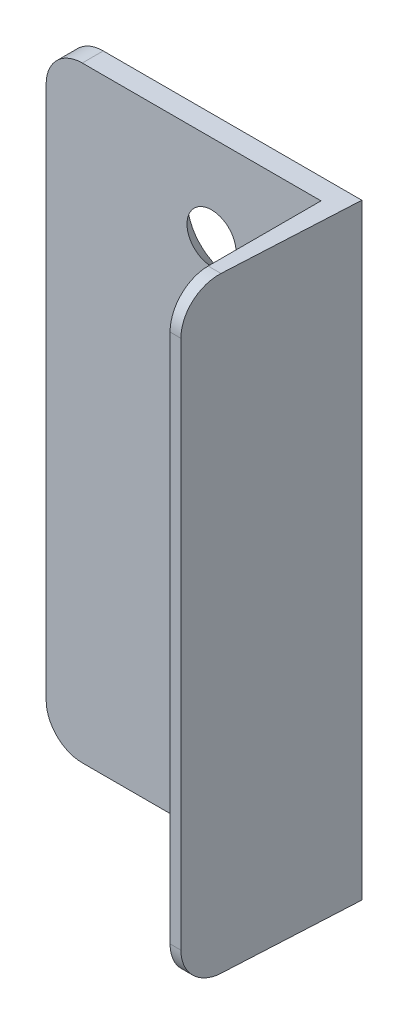
SolidWorks part; units mm, degrees
material "Brass"
ref_plane "Top Plane" through (0, 0, 0) normal (0, 0, 1) x (1, 0, 0)
ref_plane "Front Plane" through (0, 0, 0) normal (0, 1, 0) x (1, 0, 0)
ref_plane "Right Plane" through (0, 0, 0) normal (1, 0, 0) x (0, 0, -1)
sketch "Sketch1" plane through (0, 0, 0) normal (0, 0, 1) x (1, 0, 0)
  line L1 (-15.4, -41.95) -> (20.4, -41.95)
  line L2 (-20.4, -36.95) -> (-20.4, 36.95)
  line L3 (-15.4, 41.95) -> (20.4, 41.95)
  line L4 (20.4, -41.95) -> (20.4, 41.95)
  line L5 (-20.4, -41.95) -> (20.4, 41.95) construction
  line L6 (-20.4, 41.95) -> (20.4, -41.95) construction
  arc A0 (-20.4, -36.95) -> (-15.4, -41.95) centre (-15.4, -36.95) ccw
  arc A1 (-15.4, 41.95) -> (-20.4, 36.95) centre (-15.4, 36.95) ccw
  point P0 (0, 0)
  dimension "D3" = 5
  dimension "D1" = 40.8
  dimension "D2" = 83.9
extrude "Boss-Extrude1" add sketch "Sketch1" along normal blind 2.9
sketch "Sketch2" plane through (0, 0, 2.9) normal (0, 0, 1) x (1, 0, 0)
  line L0 (-15.4, -41.95) -> (20.4, -41.95) construction
  line L1 (20.4, 41.95) -> (17.65, 41.95)
  line L2 (20.4, 41.95) -> (20.4, -41.95)
  line L3 (20.4, -41.95) -> (17.65, -41.95)
  line L4 (17.65, 41.95) -> (17.65, -41.95)
  dimension "D1" = 2.75
extrude "Boss-Extrude2" add sketch "Sketch2" along normal blind 20.9
sketch "Sketch4" plane through (20.4, 0, 0) normal (1, 0, 0) x (0, 0, -1)
  line L16 (-23.8, 36.6765) -> (-23.8, 41.95)
  line L21 (-23.8, 41.95) -> (-18.5265, 41.95)
  line L22 (-23.8, -41.95) -> (-23.8, -36.6765)
  line L23 (-23.8, -41.95) -> (-18.5265, -41.95)
  arc A4 (-18.5265, -41.95) -> (-23.8, -36.6765) centre (-18.5265, -36.6765) cw
  arc A5 (-18.5265, 41.95) -> (-23.8, 36.6765) centre (-18.5265, 36.6765) ccw
  point P3 (-23.8, 41.95)
  point P8 (-23.8, -41.95)
  dimension "D1" = 5.2735
  dimension "D2" = 7.4578
  dimension "D3" = 7.4578
extrude "Cut-Extrude1" cut sketch "Sketch4" against normal blind 27.75
sketch "Sketch5" plane through (0, 0, 0) normal (0, 0, -1) x (-1, 0, 0)
  line L1 (-2.5, -41.95) -> (-2.5, 41.95) construction
  line L2 (15.4, -41.95) -> (-20.4, -41.95) construction
  line L3 (-20.4, 41.95) -> (15.4, 41.95) construction
  point P0 (-2.5, 29.8957)
  point P2 (-2.5, -29.8957)
  dimension "D1" = 30
  dimension "D2" = 30
hole_wizard "CSK for M6 Flat Head Machine Screw1" positions "Sketch5" profile "Sketch6" countersink size "M6" standard "ANSI Metric" end condition up to next
sketch "Sketch6" plane through (2.5, 29.8957, 0) normal (1, 0, 0) x (0, 1, 0)
  line L0 (0, 0) -> (0, 2.9)
  line L1 (0, 2.9) -> (3.3, 2.9)
  line L2 (3.3, 2.9) -> (3.3, 3)
  line L3 (3.3, 3) -> (6.3, 0)
  line L5 (6.3, 0) -> (0, 0)
  line L6 (-3.3, 3) -> (-6.3, 0) construction
  line L11 (0, -6.35) -> (0, 107.95) construction
  dimension "Thru Hole Dia." = 6.6
  dimension "Thru Hole Depth" = 2.9
  dimension "Near C'Sink Dia." = 12.6
  dimension "Near C'Sink Angle" = 90
sketch "Sketch8" plane through (20.4, 0, 0) normal (1, 0, 0) x (0, 0, -1)
  line L1 (0, -41.95) -> (-41.8347, -41.95)
  line L2 (0, -41.95) -> (0, 41.95)
  line L3 (0, 41.95) -> (-41.8347, 41.95)
  line L4 (-41.8347, -41.95) -> (-41.8347, 41.95)
  dimension "D1" = 41.8347
revolve "Cut-Revolve4" cut sketch "Sketch8" angle 3 about L2
